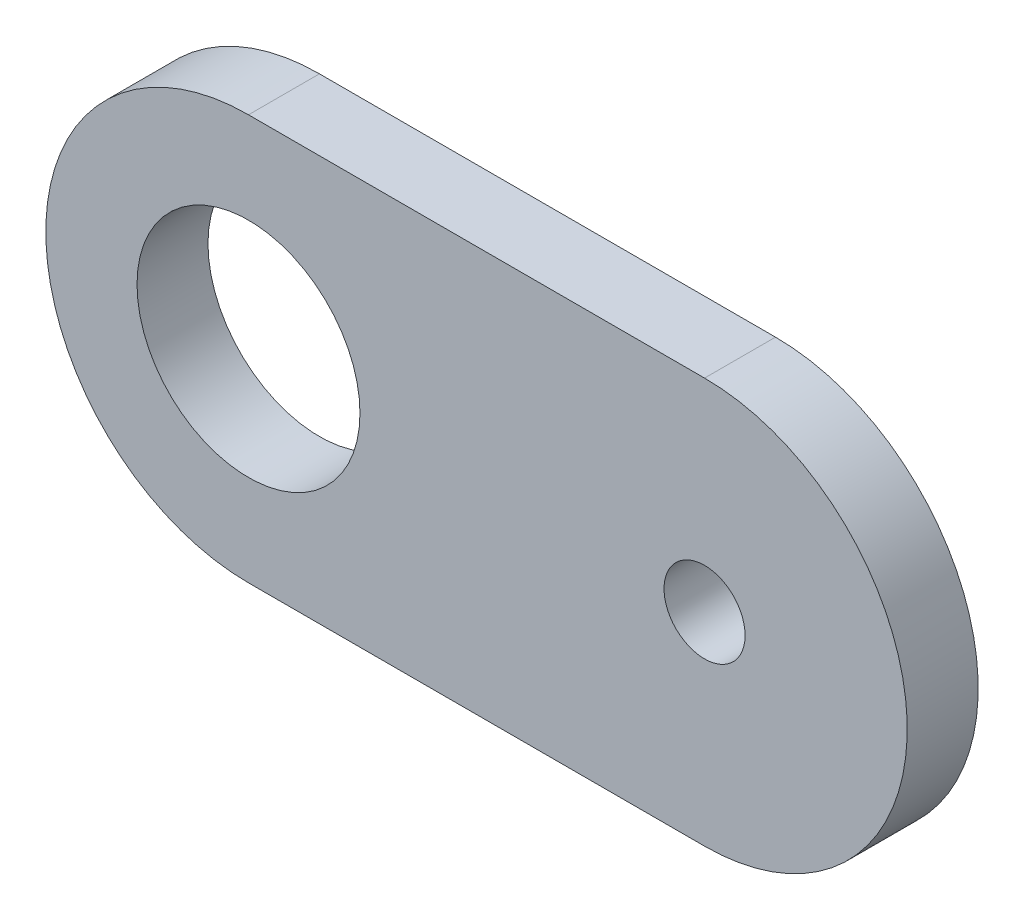
SolidWorks part; units mm, degrees
ref_plane "Front Plane" through (0, 0, 0) normal (0, 0, 1) x (1, 0, 0)
ref_plane "Top Plane" through (0, 0, 0) normal (0, 1, 0) x (1, 0, 0)
ref_plane "Right Plane" through (0, 0, 0) normal (1, 0, 0) x (0, 0, -1)
sketch "Sketch2" plane through (0, 0, 0) normal (0, 0, 1) x (1, 0, 0)
  line L1 (0, 0) -> (45, 0)
  line L3 (0, 40) -> (45, 40)
  arc A0 (0, 40) -> (0, 0) centre (0, 20) ccw
  arc A1 (45, 0) -> (45, 40) centre (45, 20) ccw
  dimension "D2" = 20
  dimension "D3" = 20
  dimension "D1" = 45
extrude "Boss-Extrude1" add sketch "Sketch2" along normal blind 7
sketch "Sketch4" plane through (0, 0, 0) normal (0, 0, -1) x (-1, 0, 0)
  line L0 (-45, 40) -> (0, 40) construction
  circle A0 centre (0, 20) radius 11
  dimension "D1" = 22
  dimension "D2" = 20
extrude "Cut-Extrude1" cut sketch "Sketch4" against normal through all
sketch "Sketch7" plane through (0, 0, 7) normal (0, 0, 1) x (1, 0, 0)
  circle A0 centre (45, 20) radius 4
  dimension "D1" = 8
extrude "Cut-Extrude2" cut sketch "Sketch7" against normal through all
